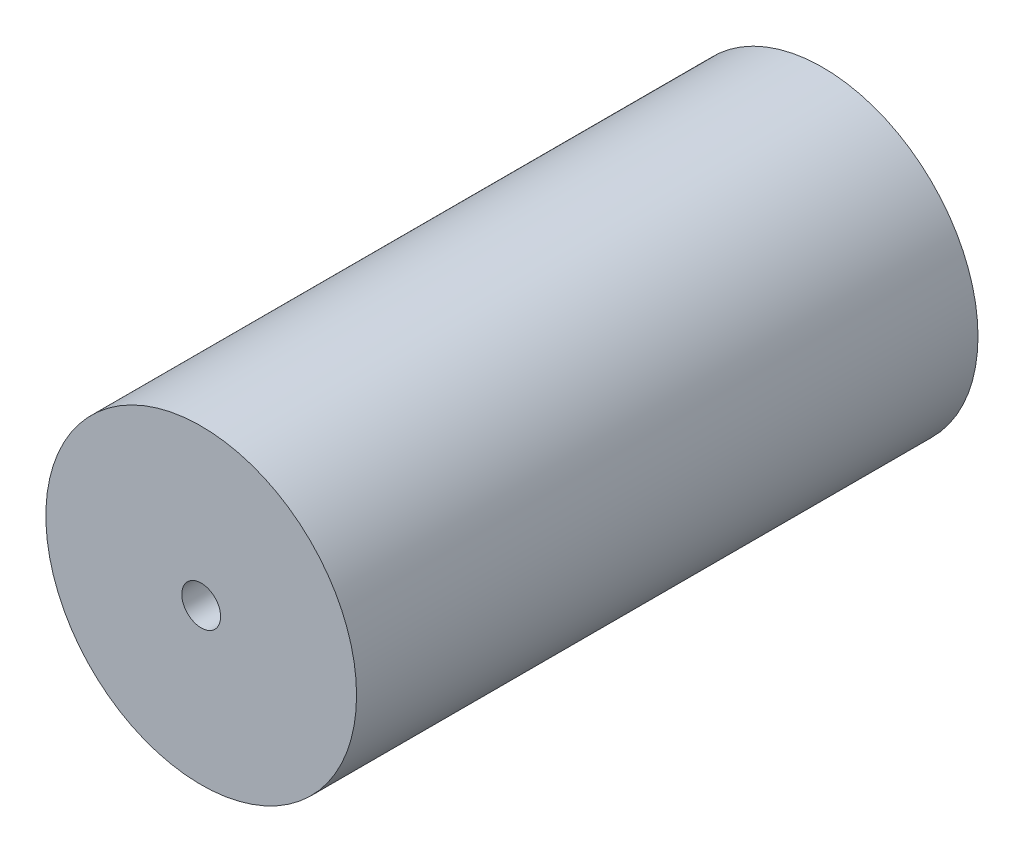
SolidWorks part; units mm, degrees
ref_plane "前视基准面" through (0, 0, 0) normal (0, 0, 1) x (1, 0, 0)
ref_plane "上视基准面" through (0, 0, 0) normal (0, 1, 0) x (1, 0, 0)
ref_plane "右视基准面" through (0, 0, 0) normal (1, 0, 0) x (0, 0, -1)
sketch "草图1" plane through (0, 0, 0) normal (0, 0, 1) x (1, 0, 0)
  circle A0 centre (0, 0) radius 20
  circle A1 centre (0, 0) radius 2.5
  dimension "D1" = 40
  dimension "D2" = 5
extrude "凸台-拉伸1" add sketch "草图1" along normal blind 80
